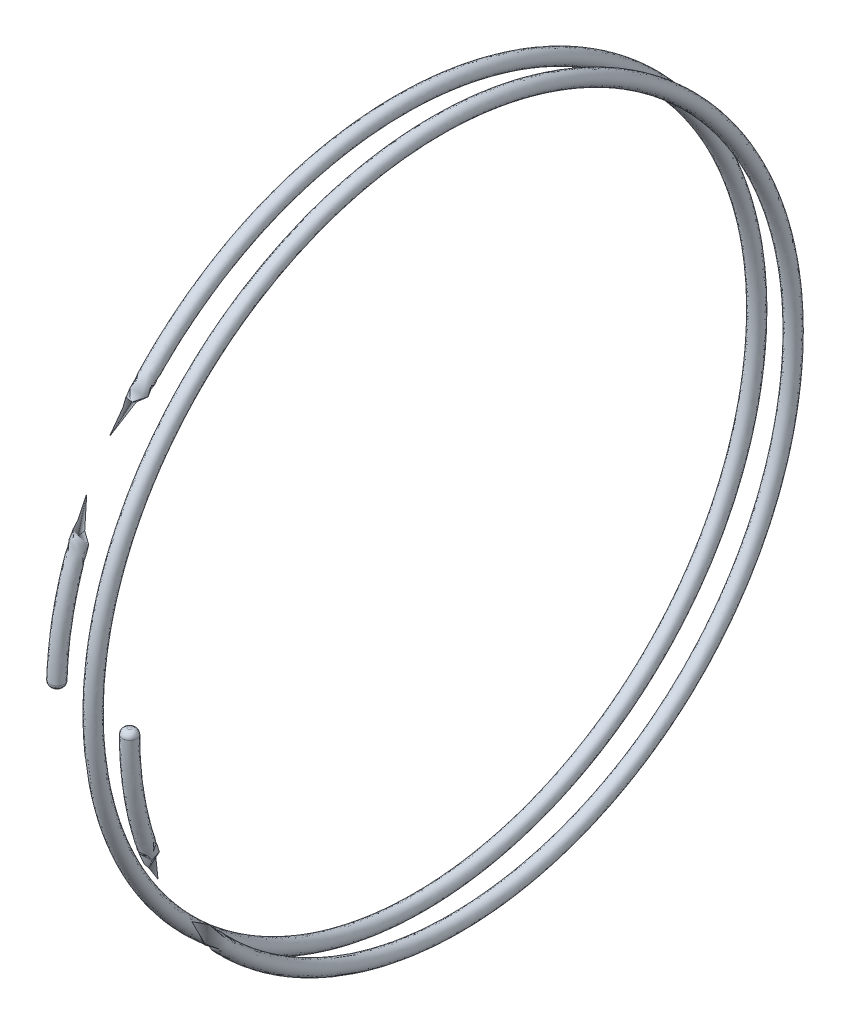
SolidWorks part; units mm, degrees
material "AISI 321 Annealed Stainless Steel (SS)"
ref_plane "Front Plane" through (0, 0, 0) normal (0, 0, 1) x (1, 0, 0)
ref_plane "Top Plane" through (0, 0, 0) normal (0, 1, 0) x (1, 0, 0)
ref_plane "Right Plane" through (0, 0, 0) normal (1, 0, 0) x (0, 0, -1)
sketch "Sketch1" plane through (0, 0, 0) normal (1, 0, 0) x (0, 0, -1)
  circle A0 centre (0, 0) radius 4.725
  dimension "D1" = 9.45
curve "Helix/Spiral1" pitch 0.505 height 1.01 turns 2
ref_plane "Plane1" through (1.01, 0, 4.725) normal (0.017, 0.9999, 0) x (-0.9892, 0.0168, 0.1459)
sketch "Sketch2" plane through (1.01, 0, 4.725) normal (0.017, 0.9999, 0) x (-0.9892, 0.0168, 0.1459)
  circle A0 centre (0, 0) radius 0.1
  dimension "D1" = 0.2
sweep "Sweep1" add profiles "Sketch2" path "Helix/Spiral1"
fillet "Fillet1" radius 0.075 2 edges at (1.11, -0.0017, 4.725) (-0.1, 0.0017, 4.725)
